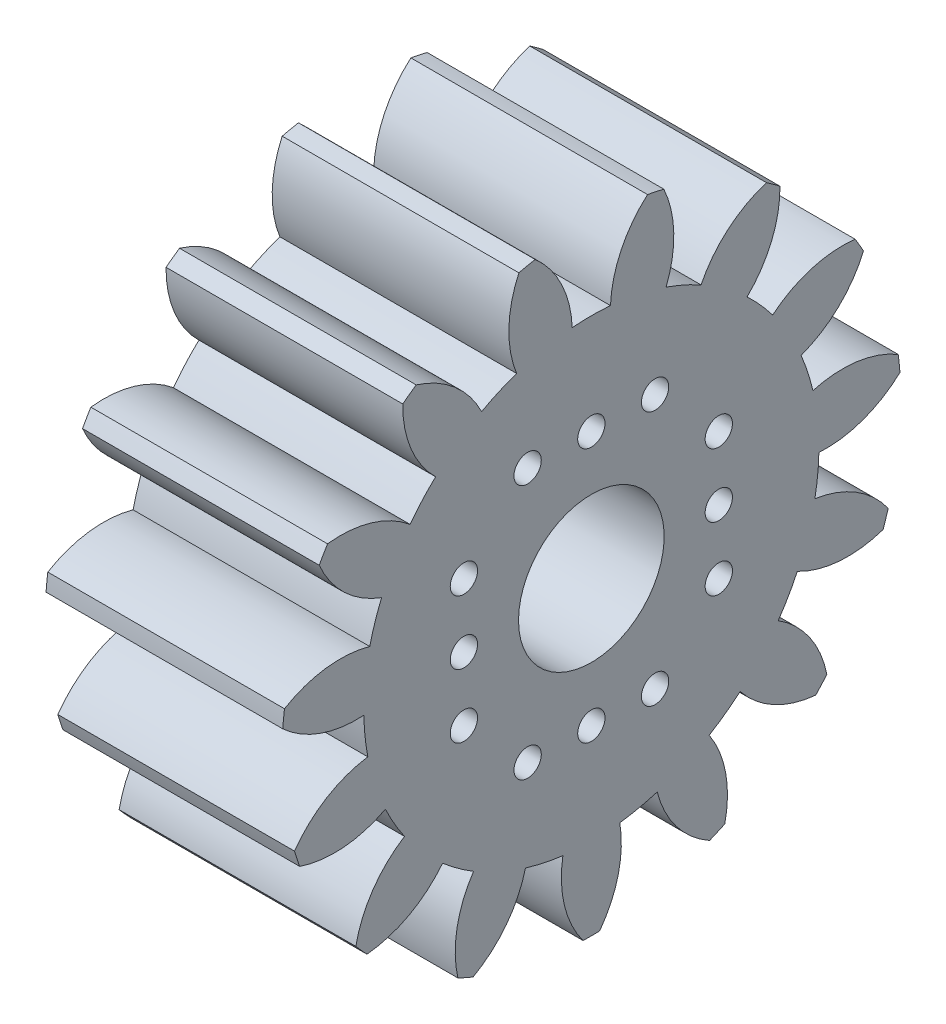
SolidWorks part; units mm, degrees
ref_plane "Plane1" through (0, 0, 0) normal (0, 0, 1) x (1, 0, 0)
ref_plane "Plane2" through (0, 0, 0) normal (0, 1, 0) x (1, 0, 0)
ref_plane "Plane3" through (0, 0, 0) normal (1, 0, 0) x (0, 0, -1)
sketch "HoldingSke" plane through (0, 0, 0) normal (0, 1, 0) x (1, 0, 0)
  line L0 (0, 0) -> (0.483, -0.1294)
  line L1 (-15, 0) -> (100, 0) construction
  line L2 (0, 0) -> (-2.1039, 2.3779)
  line L3 (0, 0) -> (-11.863, 4.5341)
  line L4 (0, 0) -> (8.3417, 2.2352)
  line L5 (0, 0) -> (-46.8476, -17.4728)
  line L6 (0, 0) -> (-10.7765, -7.2709)
  line L7 (-2.1039, 2.3779) -> (8.6586, 51.2059)
  line L8 (-76.2, 54.61) -> (-74.8, 54.61)
  line L9 (-71.009, 38.7566) -> (-53.1078, 45.2721)
  line L10 (-76.2, 71.12) -> (104.1128, 71.12)
  line L11 (0, 0) -> (-13, 0)
  line L12 (-76.2, 101.6) -> (-76.133, 101.6)
  line L13 (24.9733, 27.94) -> (52.9518, 28.4284)
  line L14 (24.9733, 27.94) -> (24.9743, 27.94)
  line L15 (24.9733, 27.94) -> (100.4006, 29.5858)
  line L16 (-63.627, -2) -> (-12.827, -2)
  circle A0 centre (0, 0) radius 4
  circle A1 centre (0, 0) radius 12.499
  circle A2 centre (0, 0) radius 37.5
  circle A3 centre (0, 0) radius 4
  dimension "MHD" = 24.998
  dimension "Hub_dia" = 75
  dimension "Bore" = 8
  dimension "MBD" = 8
  dimension "Num_teeth" = 15
  dimension "Pitch_radius" = 180.3128
  dimension "Pitch" = 0.5
  dimension "Width" = 13
  dimension "Overall_len" = 50
  dimension "Show_teeth" = 15
  dimension "Thickness" = 13
  dimension "OAL" = 50.0001
  dimension "T_dim" = 1.4
  dimension "Ap" = 20
  dimension "H" = 19.05
  dimension "Backlash" = 0.067
  dimension "Addendum_fac" = 1
  dimension "Dedendum_fac" = 1.25
  dimension "Clearance_fac" = 0.25
  dimension "Dedendum_add" = 0.001
  dimension "Module" = 2
sketch "BasProSke" plane through (0, 0, 0) normal (0, 1, 0) x (1, 0, 0)
  line L0 (-10, 0) -> (60, 0) construction
  line L1 (0, 0) -> (0, 17)
  line L2 (0, 0) -> (13, 0)
  line L3 (13, 0) -> (13, 17)
  line L4 (13, 17) -> (0, 17)
  dimension "Diameter" = 34
  dimension "Thickness" = 13
revolve "Base-Revolve" add sketch "BasProSke" angle 360 about L0
sketch "TooCutSke" plane through (0, 0, 0) normal (1, 0, 0) x (0, 0, -1)
  line L1 (0, 0) -> (0, 107) construction
  line L2 (0, 0) -> (-1.6851, 14.905) construction
  line L3 (0, 0) -> (-6.2081, 29.2069) construction
  line L4 (-1.6851, 14.905) -> (-3.1041, 14.6034) construction
  arc A0 (1.0501, 12.4548) -> (-1.0501, 12.4548) centre (0, 0) ccw
  arc A1 (3.1109, 16.7388) -> (-3.1109, 16.7388) centre (0, 0) ccw
  circle A2 centre (0, 0) radius 15 construction
  circle A3 centre (0, 0) radius 14.0954 construction
  arc A4 (-1.0501, 12.4548) -> (-3.1109, 16.7388) centre (-7.045, 12.2085) ccw
  arc A5 (3.1109, 16.7388) -> (1.0501, 12.4548) centre (7.045, 12.2085) ccw
  dimension "Root_dia" = 24.998
  dimension "Overcut_dia" = 34.0508
  dimension "Pitch_dia" = 30
  dimension "Base_dia" = 28.1908
  dimension "Flank_rad" = 6
  dimension "Half_ang" = 12
  dimension "Half_CT" = 1.4507
extrude "ToothCut" cut sketch "TooCutSke" along normal through all
fillet "Breaks" [suppressed] radius 0.04
fillet "RootFillets" [suppressed] radius 0.501
pattern_circular "TeethCuts" count 15 every 24 about axis through (-10, 0, 0) along (1, 0, 0) of "ToothCut", "RootFillets", "Breaks"
sketch "HubNeaOneSke" plane through (0, 0, 0) normal (-1, 0, 0) x (0, 0, 1)
  circle A0 centre (0, 0) radius 12.499
  dimension "Diameter" = 24.998
extrude "HubNearOne" [suppressed] add sketch "HubNeaOneSke" along normal blind 37.0001
sketch "HubNeaBotSke" plane through (0, 0, 0) normal (-1, 0, 0) x (0, 0, 1)
  circle A0 centre (0, 0) radius 12.499
  dimension "Diameter" = 24.998
extrude "HubNearBoth" [suppressed] add sketch "HubNeaBotSke" along normal blind 18.5
ref_plane "FarPln" through (13, 0, 0) normal (1, 0, 0) x (0, 0, -1)
sketch "HubFarSke" plane through (13, 0, 0) normal (1, 0, 0) x (0, 0, -1)
  circle A0 centre (0, 0) radius 12.499
  dimension "Diameter" = 24.998
extrude "HubFar" [suppressed] add sketch "HubFarSke" along normal blind 18.5
sketch "BorSke" plane through (0, 0, 0) normal (1, 0, 0) x (0, 0, -1)
  circle A0 centre (0, 0) radius 4
  dimension "Diameter" = 8
extrude "Bore" cut sketch "BorSke" along normal mid plane 100.0001
sketch "KeySke" plane through (0, 0, 0) normal (1, 0, 0) x (0, 0, -1)
  line L0 (-1.5, 0) -> (-1.5, 5.4)
  line L1 (-1.5, 5.4) -> (1.5, 5.4)
  line L2 (1.5, 5.4) -> (1.5, 0)
  line L3 (0, 0) -> (0, 34) construction
  line L4 (-1.5, 0) -> (1.5, 0)
  dimension "Offset" = 5.4
  dimension "Width" = 3
extrude "Keyway" [suppressed] cut sketch "KeySke" along normal mid plane 100.0001
pattern_circular "Keyway2" [suppressed] count 2 every 90 about axis through (-10, 0, 0) along (1, 0, 0)
sketch "Sketch1" plane through (13, 0, 0) normal (1, 0, 0) x (0, 0, -1)
  line L0 (-3.5, 7) -> (0, 7) construction
  line L1 (0, 7) -> (3.5, 7) construction
  line L2 (0, 0) -> (0, 7) construction
  circle A0 centre (-3.5, 7) radius 0.75
  circle A1 centre (0, 7) radius 0.75
  circle A2 centre (3.5, 7) radius 0.75
  dimension "D1" = 1.5
  dimension "D2" = 7
  dimension "D3" = 7
extrude "Cut-Extrude1" cut sketch "Sketch1" against normal blind 7
pattern_circular "CirPattern1" count 4 over 360 about axis through (0, 0, 0) along (1, 0, 0) of "Cut-Extrude1"
equation "' \"Module@HoldingSke\" = 6.35"
equation "' \"Num_teeth@HoldingSke\" = 12"
equation "' \"Ap@HoldingSke\" =  20"
equation "' \"Width@HoldingSke\" = 0.5 * 25.4"
equation "' \"Hub_dia@HoldingSke\"= 1 * 25.4"
equation "' \"Overall_len@HoldingSke\" = 1.0 * 25.4"
equation "' \"Bore@HoldingSke\" = 0.75 * 25.4"
equation "' \"T_dim@HoldingSke\" = 0.1 * 25.4"
equation "' \"Width@KeySke\" = 0.25 * 25.4"
equation "' \"Show_teeth@HoldingSke\" = 13"
equation "' \"Backlash@HoldingSke\" = 0.009 * 25.4"
equation "' \"Addendum_fac@HoldingSke\" = 1.0"
equation "' \"Dedendum_fac@HoldingSke\" = 1.25"
equation "' \"Dedendum_add@HoldingSke\" = 0.00005 * 25.4"
equation "' \"Clearance_fac@HoldingSke\" = 0.25"
equation "\"Pitch@HoldingSke\" = 1 / \"Module@HoldingSke\""
equation "\"Overcut_dia@TooCutSke\" = (\"Num_teeth@HoldingSke\" + 2 * \"Addendum_fac@HoldingSke\") / \"Pitch@HoldingSke\" + 0.002 * 25.4"
equation "\"Pitch_dia@TooCutSke\" = \"Num_teeth@HoldingSke\" / \"Pitch@HoldingSke\""
equation "\"Base_dia@TooCutSke\" = \"Num_teeth@HoldingSke\" / \"Pitch@HoldingSke\" * cos((\"Ap@HoldingSke\"  * 3.14159265 / 180))"
equation "\"Root_dia@TooCutSke\" = (\"Num_teeth@HoldingSke\" + 2) / \"Pitch@HoldingSke\" - 2 * (\"Addendum_fac@HoldingSke\" + \"Dedendum_fac@HoldingSke\") / \"Pitch@HoldingSke\" - \"Dedendum_add@HoldingSke\" * 2"
equation "\"Half_ang@TooCutSke\" = 180 / \"Num_teeth@HoldingSke\""
equation "\"Half_CT@TooCutSke\" = \"Num_teeth@HoldingSke\" / \"Pitch@HoldingSke\" * sin((3.14159265 / 2 / \"Num_teeth@HoldingSke\")) / 2 - 7 * \"Backlash@HoldingSke\" / 4"
equation "\"Flank_rad@TooCutSke\" = \"Num_teeth@HoldingSke\" / \"Pitch@HoldingSke\" / 5"
equation "\"Radius@RootFillets\" = \"Clearance_fac@HoldingSke\" / \"Pitch@HoldingSke\" + \"Dedendum_add@HoldingSke\""
equation "\"Break_rad@Breaks\" = 0.02 / \"Pitch@HoldingSke\""
equation "\"Thickness@HoldingSke\" = \"Width@HoldingSke\""
equation "\"OAL@HoldingSke\" = \"Thickness@HoldingSke\""
equation "\"MHD@HoldingSke\" = (\"Num_teeth@HoldingSke\" + 2) / \"Pitch@HoldingSke\" - 2 * (\"Addendum_fac@HoldingSke\" + \"Dedendum_fac@HoldingSke\")  / \"Pitch@HoldingSke\" - \"Dedendum_add@HoldingSke\" * 2"
equation "\"MBD@HoldingSke\" = (\"Num_teeth@HoldingSke\" + 2) / \"Pitch@HoldingSke\" - 2 * (\"Addendum_fac@HoldingSke\" + \"Dedendum_fac@HoldingSke\")  / \"Pitch@HoldingSke\" - \"Dedendum_add@HoldingSke\" * 2 - 0.002 * 25.4"
equation "\"MHD@HoldingSke\" = ((sgn( \"MHD@HoldingSke\" - \"Hub_dia@HoldingSke\" )-1)*( \"MHD@HoldingSke\" - \"Hub_dia@HoldingSke\" ))/-2+ \"Hub_dia@HoldingSke\""
equation "\"MBD@HoldingSke\" = ((sgn( \"MBD@HoldingSke\" - \"Bore@HoldingSke\" )-1)*( \"MBD@HoldingSke\" - \"Bore@HoldingSke\" ))/-2+ \"Bore@HoldingSke\""
equation "\"OAL@HoldingSke\" = ((sgn( \"OAL@HoldingSke\" - \"Overall_len@HoldingSke\" )+1)*( \"OAL@HoldingSke\" - \"Overall_len@HoldingSke\" ))/2 + \"Overall_len@HoldingSke\" + 0.000002 * 25.4"
equation "\"Num_teeth@TeethCuts\" = int( \"Show_teeth@HoldingSke\" ) + 1"
equation "\"Num_teeth@TeethCuts\" = ((sgn( \"Num_teeth@TeethCuts\" - \"Num_teeth@HoldingSke\" )-1)*( \"Num_teeth@TeethCuts\" - \"Num_teeth@HoldingSke\" ))/-2+ \"Num_teeth@HoldingSke\""
equation "\"Num_teeth@TeethCuts\" = ((sgn( \"Num_teeth@TeethCuts\" - 2.0)+1)*( \"Num_teeth@TeethCuts\" - 2.0))/2 +2.0"
equation "\"Angle@TeethCuts\" = 360.0 / \"Num_teeth@HoldingSke\""
equation "\"Diameter@BasProSke\" = (\"Num_teeth@HoldingSke\" + 2 * \"Addendum_fac@HoldingSke\") / \"Pitch@HoldingSke\""
equation "\"Thickness@BasProSke\"  = \"Thickness@HoldingSke\""
equation "' \"Fillet_rad@BasProSke\" =  \"Thickness@HoldingSke\" * 0.05"
equation "\"MHD@HoldingSke\" = ((sgn( \"MHD@HoldingSke\" - \"Root_dia@TooCutSke\" )-1)*( \"MHD@HoldingSke\" - \"Root_dia@TooCutSke\" ))/-2+ \"Root_dia@TooCutSke\""
equation "\"Diameter@HubNeaOneSke\" = \"MHD@HoldingSke\""
equation "\"Length@HubNearOne\" = \"OAL@HoldingSke\" - \"Thickness@BasProSke\""
equation "\"Diameter@HubNeaBotSke\" = \"MHD@HoldingSke\""
equation "\"Length@HubNearBoth\" = ( \"OAL@HoldingSke\" - \"Thickness@BasProSke\" ) / 2.0"
equation "\"Thickness@FarPln\" = \"Thickness@BasProSke\""
equation "\"Diameter@HubFarSke\" = \"MHD@HoldingSke\""
equation "\"Length@HubFar\" = ( \"OAL@HoldingSke\" - \"Thickness@BasProSke\" ) / 2.0"
equation "\"Diameter@BorSke\" = \"MBD@HoldingSke\""
equation "\"D1@Bore\" = \"OAL@HoldingSke\" * 2.0"
equation "\"D1@Keyway\" = \"OAL@HoldingSke\" * 2.0"
equation "\"Offset@KeySke\" = \"T_dim@HoldingSke\" + \"MBD@HoldingSke\" / 2.0"
